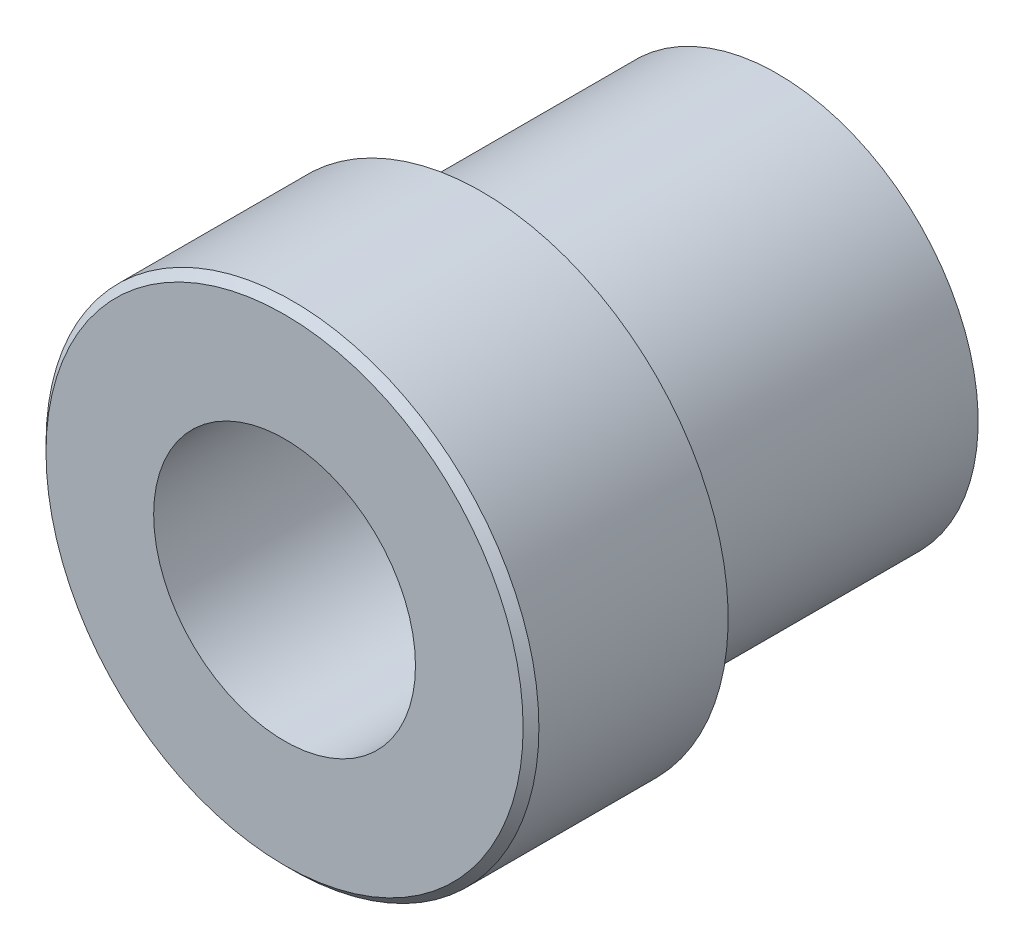
SolidWorks part; units mm, degrees
material "AISI 4130 Steel, annealed at 865C"
ref_plane "Front" through (0, 0, 0) normal (0, 0, 1) x (1, 0, 0)
ref_plane "Top" through (0, 0, 0) normal (0, 1, 0) x (1, 0, 0)
ref_plane "Right" through (0, 0, 0) normal (1, 0, 0) x (0, 0, -1)
sketch "Sketch1" plane through (0, 0, 0) normal (0, 0, 1) x (1, 0, 0)
  circle A0 centre (0, 0) radius 7.9375
extrude "Boss-Extrude1" add sketch "Sketch1" along normal blind 15.875
chamfer "Chamfer1" distance 0.254 angle 45 1 edges at (7.9375, 0, 15.875)
sketch "Sketch2" plane through (0, 0, 0) normal (0, 0, -1) x (-1, 0, 0)
  circle A0 centre (0, 0) radius 6.4643
  circle A1 centre (0, 0) radius 7.9375 construction
  dimension "D1" = 1.4732
extrude "Cut-Extrude1" cut sketch "Sketch2" against normal blind 9.525 flip side to cut
hole_wizard "Tap Drill for 3/8-24 Tap1" positions "Sketch5" profile "Sketch6" hole size "3/8-24" standard "ANSI Inch" end condition through all
sketch "Sketch5" plane through (0, 0, 15.875) normal (0, 0, 1) x (1, 0, 0)
  point P0 (0, 0)
sketch "Sketch6" plane through (0, 0, 15.875) normal (1, 0, 0) x (0, -1, 0)
  line L0 (0, 0) -> (0, 15.875)
  line L1 (0, 15.875) -> (4.2164, 15.875)
  line L2 (4.2164, 15.875) -> (4.2164, 0)
  line L5 (4.2164, 0) -> (0, 0)
  line L11 (0, -6.35) -> (0, 107.95) construction
  dimension "Thru Hole Dia." = 8.4328
  dimension "Thru Hole Depth" = 15.875
hole_wizard "Tap Drill for 5/16-18 Tap1" positions "Sketch7" profile "Sketch8" hole size "5/16-18" standard "ANSI Inch"
sketch "Sketch7" plane through (0, 0, 15.875) normal (0, 0, 1) x (1, 0, 0)
  point P0 (0, 0)
sketch "Sketch8" plane through (0, 0, 15.875) normal (1, 0, 0) x (0, -1, 0)
  line L0 (0, 0) -> (0, 15.875)
  line L1 (0, 15.875) -> (3.2639, 15.875)
  line L2 (3.2639, 15.875) -> (3.2639, 0)
  line L5 (3.2639, 0) -> (0, 0)
  line L11 (0, -6.35) -> (0, 107.95) construction
  dimension "Thru Hole Dia." = 6.5278
  dimension "Thru Hole Depth" = 15.875
hole_wizard "Tap Drill for 1/4-28 Tap1" positions "Sketch9" profile "Sketch10" hole size "1/4-28" standard "ANSI Inch"
sketch "Sketch9" plane through (0, 0, 15.875) normal (0, 0, 1) x (1, 0, 0)
  point P0 (0, 0)
sketch "Sketch10" plane through (0, 0, 15.875) normal (1, 0, 0) x (0, -1, 0)
  line L0 (0, 0) -> (0, 15.875)
  line L1 (0, 15.875) -> (2.7051, 15.875)
  line L2 (2.7051, 15.875) -> (2.7051, 0)
  line L5 (2.7051, 0) -> (0, 0)
  line L11 (0, -6.35) -> (0, 107.95) construction
  dimension "Thru Hole Dia." = 5.4102
  dimension "Thru Hole Depth" = 15.875
equation "\"Tube Radius\"= 5 / 16in"
equation "\"Wall Thickness\"= 0.058"
equation "\"D1@Sketch1\"= 2 * \"Tube Radius\""
equation "\"D1@Sketch2\" = \"Wall Thickness\""
